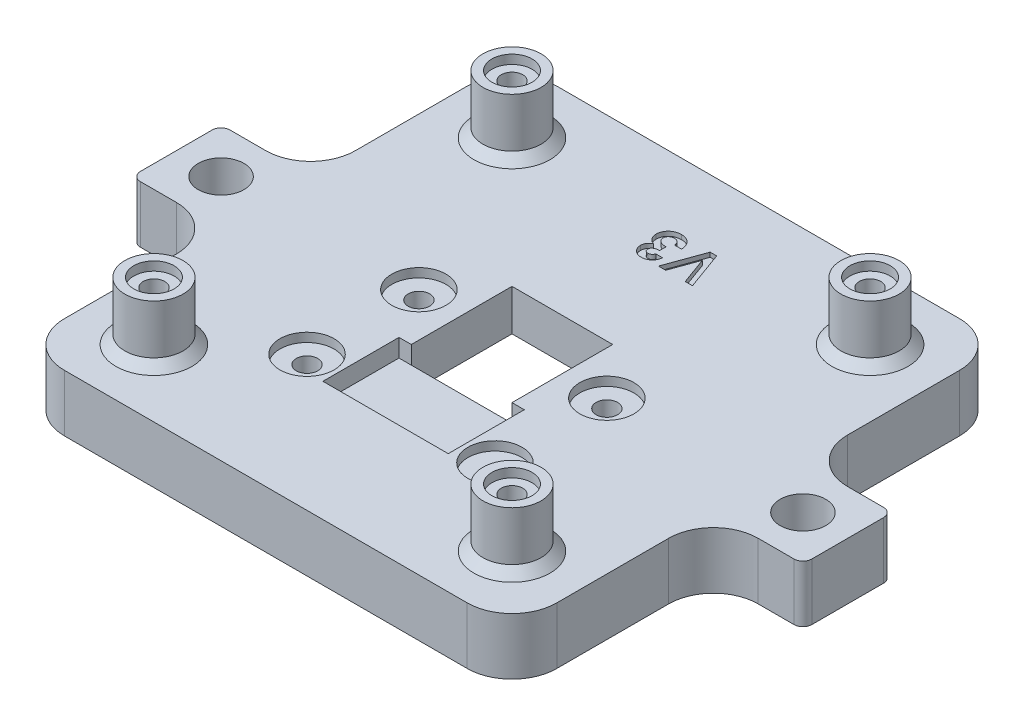
SolidWorks part; units mm, degrees
ref_plane "Front Plane" through (0, 0, 0) normal (0, 0, 1) x (1, 0, 0)
ref_plane "Top Plane" through (0, 0, 0) normal (0, 1, 0) x (1, 0, 0)
ref_plane "Right Plane" through (0, 0, 0) normal (1, 0, 0) x (0, 0, -1)
sketch "Sketch1" plane through (0, 0, 0) normal (0, 1, 0) x (1, 0, 0)
  line L1 (-27.5, 27.5) -> (27.5, 27.5)
  line L2 (-27.5, 27.5) -> (-27.5, -27.5)
  line L3 (-27.5, -27.5) -> (27.5, -27.5)
  line L4 (27.5, 27.5) -> (27.5, -27.5)
  line L5 (-27.5, 27.5) -> (27.5, -27.5) construction
  line L6 (-27.5, -27.5) -> (27.5, 27.5) construction
  point P0 (0, 0)
  dimension "D1" = 55
  dimension "D2" = 55
extrude "Boss-Extrude1" add sketch "Sketch1" along normal blind 6.35
sketch "Sketch2" plane through (0, 6.35, 0) normal (0, 1, 0) x (1, 0, 0)
  line L1 (-5.625, -5.625) -> (5.625, -5.625)
  line L2 (-5.625, -5.625) -> (-5.625, 5.625)
  line L3 (-5.625, 5.625) -> (5.625, 5.625)
  line L4 (5.625, -5.625) -> (5.625, 5.625)
  line L5 (-5.625, -5.625) -> (5.625, 5.625) construction
  line L6 (-5.625, 5.625) -> (5.625, -5.625) construction
  point P0 (0, 0)
  dimension "D1" = 11.25
extrude "Cut-Extrude1" cut sketch "Sketch2" against normal through all
sketch "Sketch3" plane through (0, 6.35, 0) normal (0, 1, 0) x (1, 0, 0)
  line L0 (0, 0) -> (0, 2.7158) construction
  line L1 (-7, -5.625) -> (7, -5.625)
  line L2 (-7, -5.625) -> (-7, -14.125)
  line L3 (-7, -14.125) -> (7, -14.125)
  line L4 (7, -5.625) -> (7, -14.125)
  line L6 (-5.625, -5.625) -> (5.625, -5.625) construction
  point P5 (0, -5.625)
  dimension "D1" = 14
  dimension "D2" = 8.5
extrude "Cut-Extrude2" cut sketch "Sketch3" against normal blind 2
sketch "Sketch4" plane through (0, 0, 0) normal (0, 1, 0) x (1, 0, 0)
  line L0 (0, 0) -> (0, 9.1234) construction
  line L2 (-12.5, 9.462) -> (12.5, 9.462) construction
  line L3 (-12.5, 9.462) -> (-12.5, -14.4) construction
  line L4 (-12.5, -14.4) -> (12.5, -14.4) construction
  line L5 (12.5, 9.462) -> (12.5, -14.4) construction
  point P7 (0, 9.462)
  point P8 (10.5, -12.4)
  point P9 (-10.5, -12.4)
  point P10 (-10.5, 0.1)
  point P11 (10.5, 0.1)
  dimension "D1" = 14.4
  dimension "D2" = 23.862
  dimension "D3" = 25
  dimension "D4" = 2
  dimension "D5" = 2
  dimension "D6" = 14.5
hole_wizard "CBORE for M2 SHCS2" positions "Sketch4" profile "Sketch15" counterbore size "M2" standard "ANSI Metric" end condition up to next
sketch "Sketch15" plane through (10.5, 0, -0.1) normal (1, 0, 0) x (0, 0, -1)
  line L0 (0, 0) -> (0, 6.35)
  line L1 (0, 6.35) -> (1.2, 6.35)
  line L3 (1.2, 6.35) -> (1.2, 2)
  line L4 (1.2, 2) -> (2.2, 2)
  line L5 (2.2, 2) -> (2.2, 0)
  line L7 (2.2, 0) -> (0, 0)
  line L11 (0, -6.35) -> (0, 107.95) construction
  dimension "Thru Hole Dia." = 2.4
  dimension "Thru Hole Depth" = 6.35
  dimension "C'Bore Dia." = 4.4
  dimension "C'Bore Depth" = 2
sketch "Sketch6" plane through (0, 6.35, 0) normal (0, 1, 0) x (1, 0, 0)
  line L1 (-20, -20) -> (20, -20) construction
  line L2 (-20, -20) -> (-20, 20) construction
  line L3 (-20, 20) -> (20, 20) construction
  line L4 (20, -20) -> (20, 20) construction
  line L5 (-20, -20) -> (20, 20) construction
  line L6 (-20, 20) -> (20, -20) construction
  circle A0 centre (-20, 20) radius 3.25
  circle A1 centre (20, 20) radius 3.25
  circle A2 centre (20, -20) radius 3.25
  circle A3 centre (-20, -20) radius 3.25
  point P0 (0, 0)
  dimension "D2" = 6.5
  dimension "D1" = 40
extrude "Boss-Extrude2" add sketch "Sketch6" along normal blind 6.5
sketch "Sketch10" plane through (0, 0, 0) normal (0, -1, 0) x (1, 0, 0)
  circle A0 centre (20, 20) radius 3.25 construction
  circle A1 centre (20, -20) radius 3.25 construction
  circle A2 centre (-20, -20) radius 3.25 construction
  circle A3 centre (-20, 20) radius 3.25 construction
  circle A4 centre (20, 20) radius 3.25 construction
  circle A5 centre (20, -20) radius 3.25 construction
  circle A6 centre (-20, -20) radius 3.25 construction
  circle A7 centre (-20, 20) radius 3.25 construction
  point P13 (-20, 20)
  point P14 (20, 20)
  point P15 (20, -20)
  point P16 (-20, -20)
hole_wizard "CBORE for M2 SHCS1" positions "Sketch10" profile "Sketch11" counterbore size "M2" standard "ANSI Metric" end condition through all
sketch "Sketch11" plane through (-20, 0, -20) normal (1, 0, 0) x (0, 0, -1)
  line L0 (0, 0) -> (0, 12.85)
  line L1 (0, 12.85) -> (1.2, 12.85)
  line L3 (1.2, 12.85) -> (1.2, 2)
  line L4 (1.2, 2) -> (2.2, 2)
  line L5 (2.2, 2) -> (2.2, 0)
  line L7 (2.2, 0) -> (0, 0)
  line L11 (0, -6.35) -> (0, 107.95) construction
  dimension "Thru Hole Dia." = 2.4
  dimension "Thru Hole Depth" = 12.85
  dimension "C'Bore Dia." = 4.4
  dimension "C'Bore Depth" = 2
sketch "Sketch12" plane through (0, 0, 0) normal (0, 0, 1) x (1, 0, 0)
  line L0 (27.5, 6.35) -> (27.5, 0) construction
  line L1 (-27.5, 6.35) -> (27.5, 6.35)
  line L2 (-27.5, 6.35) -> (-27.5, 12.85)
  line L3 (-27.5, 12.85) -> (27.5, 12.85)
  line L4 (27.5, 6.35) -> (27.5, 12.85)
  line L5 (-16.75, 12.85) -> (-23.25, 12.85) construction
extrude "Cut-Extrude3" [suppressed] cut sketch "Sketch12" against normal through all and the other way through all
sketch "Sketch13" plane through (0, 6.35, 0) normal (0, 1, 0) x (1, 0, 0)
  line L0 (0, 0) -> (0, -5.9289) construction
  circle A0 centre (-10.5, -12.4) radius 3.025
  circle A1 centre (-10.5, 0.1) radius 3.025
  circle A2 centre (10.5, -12.4) radius 3.025
  circle A3 centre (10.5, 0.1) radius 3.025
  circle A5 centre (-10.5, -12.4) radius 1.2 construction
  circle A6 centre (-10.5, 0.1) radius 1.2 construction
  dimension "D1" = 6.05
extrude "Cut-Extrude4" cut sketch "Sketch13" against normal blind 1
chamfer "Chamfer1" distance 1.75 angle 45 4 edges at (0, 0, -5.625) (5.625, 0, 0) (-5.625, 0, 0) (0, 0, 5.625)
sketch "Sketch14" plane through (0, 6.35, 0) normal (0, 1, 0) x (1, 0, 0)
  circle A0 centre (0, 0) radius 5.2973
sketch "Sketch16" plane through (0, 0, 0) normal (0, -1, 0) x (1, 0, 0)
  line L0 (0, 0) -> (30.2977, 0) construction
  line L1 (27.5, 27.5) -> (27.5, -27.5) construction
  line L2 (27.5, -5) -> (37.5, -5)
  line L3 (27.5, -5) -> (27.5, 5)
  line L4 (27.5, 5) -> (37.5, 5)
  line L5 (37.5, -5) -> (37.5, 5)
  line L6 (0, 0) -> (0, -32.0424) construction
  line L7 (-27.5, 5) -> (-37.5, 5)
  line L8 (-37.5, -5) -> (-37.5, 5)
  line L9 (-27.5, -5) -> (-37.5, -5)
  line L10 (-27.5, -5) -> (-27.5, 5)
  point P9 (27.5, 0)
  dimension "D1" = 10
  dimension "D2" = 10
extrude "Boss-Extrude3" add sketch "Sketch16" against normal up to surface (6.35 mm away) up to face at (-10.5, 6.35, 2.925)
sketch "Sketch17" plane through (0, 0, 0) normal (0, -1, 0) x (1, 0, 0)
  line L0 (37.5, 0) -> (27.5, 0) construction
  line L1 (37.5, -5) -> (37.5, 5) construction
  line L2 (27.5, -5) -> (27.5, -27.5) construction
  line L3 (0, 0) -> (0, -11.6553) construction
  circle A0 centre (32.5, 0) radius 2.55
  circle A1 centre (-32.5, 0) radius 2.55
  point P8 (32.5, 0)
  point P10 (-32.5, 0)
  point P17 (35.05, 0)
  dimension "D1" = 5.1
extrude "Cut-Extrude6" cut sketch "Sketch17" against normal through all
fillet "Fillet1" radius 5 8 edges at (27.5, 3.175, 5) (27.5, 3.175, -5) (-27.5, 3.175, 5) (-27.5, 3.175, -5) (-27.5, 3.175, -27.5) (-27.5, 3.175, 27.5) (27.5, 3.175, 27.5) (27.5, 3.175, -27.5)
fillet "Fillet2" radius 1 4 edges at (-37.5, 3.175, -5) (-37.5, 3.175, 5) (37.5, 3.175, 5) (37.5, 3.175, -5)
sketch "Sketch18" plane through (0, 12.85, 0) normal (0, 1, 0) x (1, 0, 0)
  circle A0 centre (-20, 20) radius 2.25
  circle A1 centre (-20, -20) radius 2.25
  circle A2 centre (20, 20) radius 2.25
  circle A3 centre (20, -20) radius 2.25
  dimension "D1" = 4.5
extrude "Cut-Extrude7" cut sketch "Sketch18" against normal blind 1
sketch "Sketch19" plane through (0, 6.35, 0) normal (0, 1, 0) x (1, 0, 0)
  line L0 (-16.75, 20) -> (16.75, 20) construction
  circle A0 centre (-20, 20) radius 3.25 construction
  circle A1 centre (-20, 20) radius 3.25 construction
  circle A2 centre (20, 20) radius 3.25 construction
  text T0 "<b>V3 </b>" font "Century Gothic" height in points 16
extrude "Cut-Extrude8" cut sketch "Sketch19" against normal blind 0.5
chamfer "Chamfer2" distance 1 angle 45 4 edges at (20, 6.35, 23.25) (20, 6.35, -16.75) (-20, 6.35, -16.75) (-20, 6.35, 23.25)
equation "\"D2@Sketch1\"=\"D1@Sketch1\""
